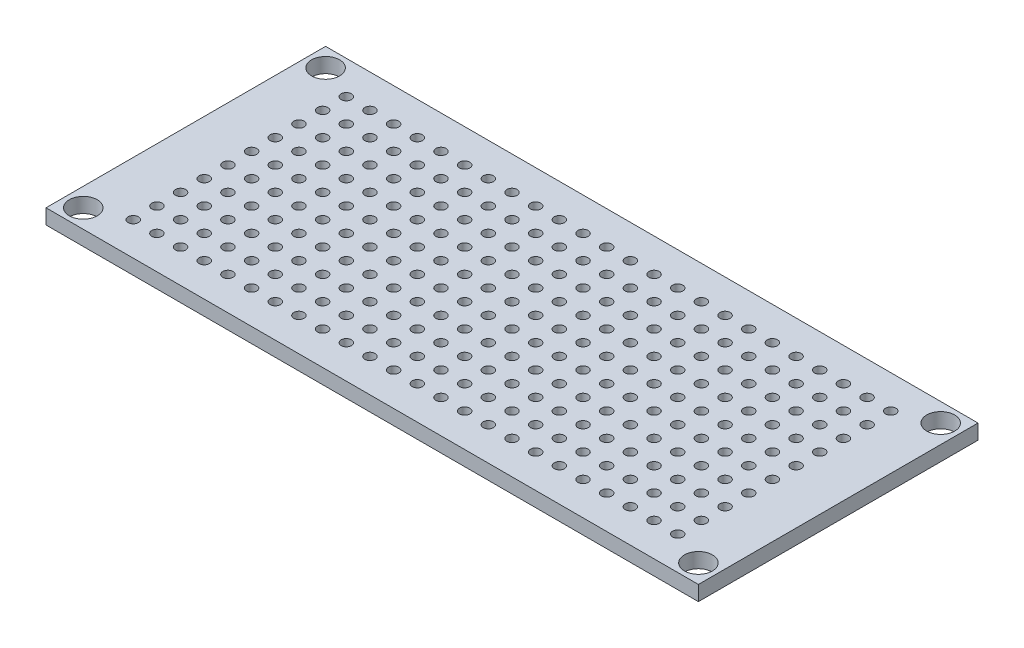
SolidWorks part; units mm, degrees
ref_plane "Front Plane" through (0, 0, 0) normal (0, 0, 1) x (1, 0, 0)
ref_plane "Top Plane" through (0, 0, 0) normal (0, 1, 0) x (1, 0, 0)
ref_plane "Right Plane" through (0, 0, 0) normal (1, 0, 0) x (0, 0, -1)
sketch "Sketch1" plane through (0, 0, 0) normal (0, 1, 0) x (1, 0, 0)
  line L0 (0, 15) -> (0, -15) construction
  line L1 (-35, 15) -> (35, 15)
  line L2 (-35, 15) -> (-35, -15)
  line L3 (-35, -15) -> (35, -15)
  line L4 (35, 15) -> (35, -15)
  line L5 (-35, 15) -> (35, -15) construction
  line L6 (-35, -15) -> (35, 15) construction
  line L7 (-35, 0) -> (35, 0) construction
  circle A0 centre (-33, 13) radius 1.5
  circle A1 centre (33, 13) radius 1.5
  circle A2 centre (33, -13) radius 1.5
  circle A3 centre (-33, -13) radius 1.5
  point P0 (0, 0)
  dimension "D5" = 3
  dimension "D1" = 70
  dimension "D2" = 30
  dimension "D3" = 66
  dimension "D4" = 26
extrude "Boss-Extrude1" add sketch "Sketch1" along normal blind 1.6
sketch "Sketch2" plane through (0, 1.6, 0) normal (0, 1, 0) x (1, 0, 0)
  line L0 (29.21, 11.43) -> (29.21, -11.43) construction
  line L1 (-35, 0) -> (35, 0) construction
  line L2 (-35, 15) -> (-35, -15) construction
  line L3 (35, -15) -> (35, 15) construction
  line L4 (-29.21, -11.43) -> (29.21, -11.43) construction
  line L5 (0, 15) -> (0, -15) construction
  line L6 (35, 15) -> (-35, 15) construction
  line L7 (-35, -15) -> (35, -15) construction
  line L8 (-29.21, 8.89) -> (-29.21, 11.43) construction
  line L9 (-29.21, 11.43) -> (-26.67, 11.43) construction
  circle A0 centre (-29.21, 11.43) radius 0.55
  circle A1 centre (-26.67, 11.43) radius 0.55
  circle A2 centre (-24.13, 11.43) radius 0.55
  circle A3 centre (-21.59, 11.43) radius 0.55
  circle A4 centre (-19.05, 11.43) radius 0.55
  circle A5 centre (-16.51, 11.43) radius 0.55
  circle A6 centre (-13.97, 11.43) radius 0.55
  circle A7 centre (-11.43, 11.43) radius 0.55
  circle A8 centre (-8.89, 11.43) radius 0.55
  circle A9 centre (-6.35, 11.43) radius 0.55
  circle A10 centre (-3.81, 11.43) radius 0.55
  circle A11 centre (-1.27, 11.43) radius 0.55
  circle A12 centre (1.27, 11.43) radius 0.55
  circle A13 centre (3.81, 11.43) radius 0.55
  circle A14 centre (6.35, 11.43) radius 0.55
  circle A15 centre (8.89, 11.43) radius 0.55
  circle A16 centre (11.43, 11.43) radius 0.55
  circle A17 centre (13.97, 11.43) radius 0.55
  circle A18 centre (16.51, 11.43) radius 0.55
  circle A19 centre (19.05, 11.43) radius 0.55
  circle A20 centre (21.59, 11.43) radius 0.55
  circle A21 centre (24.13, 11.43) radius 0.55
  circle A22 centre (26.67, 11.43) radius 0.55
  circle A23 centre (29.21, 11.43) radius 0.55
  circle A24 centre (-26.67, 8.89) radius 0.55
  circle A25 centre (-24.13, 8.89) radius 0.55
  circle A26 centre (-21.59, 8.89) radius 0.55
  circle A27 centre (-19.05, 8.89) radius 0.55
  circle A28 centre (-16.51, 8.89) radius 0.55
  circle A29 centre (-13.97, 8.89) radius 0.55
  circle A30 centre (-11.43, 8.89) radius 0.55
  circle A31 centre (-8.89, 8.89) radius 0.55
  circle A32 centre (-6.35, 8.89) radius 0.55
  circle A33 centre (-3.81, 8.89) radius 0.55
  circle A34 centre (-1.27, 8.89) radius 0.55
  circle A35 centre (1.27, 8.89) radius 0.55
  circle A36 centre (3.81, 8.89) radius 0.55
  circle A37 centre (6.35, 8.89) radius 0.55
  circle A38 centre (8.89, 8.89) radius 0.55
  circle A39 centre (11.43, 8.89) radius 0.55
  circle A40 centre (13.97, 8.89) radius 0.55
  circle A41 centre (16.51, 8.89) radius 0.55
  circle A42 centre (19.05, 8.89) radius 0.55
  circle A43 centre (21.59, 8.89) radius 0.55
  circle A44 centre (24.13, 8.89) radius 0.55
  circle A45 centre (26.67, 8.89) radius 0.55
  circle A46 centre (29.21, 8.89) radius 0.55
  circle A47 centre (-26.67, 6.35) radius 0.55
  circle A48 centre (-24.13, 6.35) radius 0.55
  circle A49 centre (-21.59, 6.35) radius 0.55
  circle A50 centre (-19.05, 6.35) radius 0.55
  circle A51 centre (-16.51, 6.35) radius 0.55
  circle A52 centre (-13.97, 6.35) radius 0.55
  circle A53 centre (-11.43, 6.35) radius 0.55
  circle A54 centre (-8.89, 6.35) radius 0.55
  circle A55 centre (-6.35, 6.35) radius 0.55
  circle A56 centre (-3.81, 6.35) radius 0.55
  circle A57 centre (-1.27, 6.35) radius 0.55
  circle A58 centre (1.27, 6.35) radius 0.55
  circle A59 centre (3.81, 6.35) radius 0.55
  circle A60 centre (6.35, 6.35) radius 0.55
  circle A61 centre (8.89, 6.35) radius 0.55
  circle A62 centre (11.43, 6.35) radius 0.55
  circle A63 centre (13.97, 6.35) radius 0.55
  circle A64 centre (16.51, 6.35) radius 0.55
  circle A65 centre (19.05, 6.35) radius 0.55
  circle A66 centre (21.59, 6.35) radius 0.55
  circle A67 centre (24.13, 6.35) radius 0.55
  circle A68 centre (26.67, 6.35) radius 0.55
  circle A69 centre (29.21, 6.35) radius 0.55
  circle A70 centre (-26.67, 3.81) radius 0.55
  circle A71 centre (-24.13, 3.81) radius 0.55
  circle A72 centre (-21.59, 3.81) radius 0.55
  circle A73 centre (-19.05, 3.81) radius 0.55
  circle A74 centre (-16.51, 3.81) radius 0.55
  circle A75 centre (-13.97, 3.81) radius 0.55
  circle A76 centre (-11.43, 3.81) radius 0.55
  circle A77 centre (-8.89, 3.81) radius 0.55
  circle A78 centre (-6.35, 3.81) radius 0.55
  circle A79 centre (-3.81, 3.81) radius 0.55
  circle A80 centre (-1.27, 3.81) radius 0.55
  circle A81 centre (1.27, 3.81) radius 0.55
  circle A82 centre (3.81, 3.81) radius 0.55
  circle A83 centre (6.35, 3.81) radius 0.55
  circle A84 centre (8.89, 3.81) radius 0.55
  circle A85 centre (11.43, 3.81) radius 0.55
  circle A86 centre (13.97, 3.81) radius 0.55
  circle A87 centre (16.51, 3.81) radius 0.55
  circle A88 centre (19.05, 3.81) radius 0.55
  circle A89 centre (21.59, 3.81) radius 0.55
  circle A90 centre (24.13, 3.81) radius 0.55
  circle A91 centre (26.67, 3.81) radius 0.55
  circle A92 centre (29.21, 3.81) radius 0.55
  circle A93 centre (-26.67, 1.27) radius 0.55
  circle A94 centre (-24.13, 1.27) radius 0.55
  circle A95 centre (-21.59, 1.27) radius 0.55
  circle A96 centre (-19.05, 1.27) radius 0.55
  circle A97 centre (-16.51, 1.27) radius 0.55
  circle A98 centre (-13.97, 1.27) radius 0.55
  circle A99 centre (-11.43, 1.27) radius 0.55
  circle A100 centre (-8.89, 1.27) radius 0.55
  circle A101 centre (-6.35, 1.27) radius 0.55
  circle A102 centre (-3.81, 1.27) radius 0.55
  circle A103 centre (-1.27, 1.27) radius 0.55
  circle A104 centre (1.27, 1.27) radius 0.55
  circle A105 centre (3.81, 1.27) radius 0.55
  circle A106 centre (6.35, 1.27) radius 0.55
  circle A107 centre (8.89, 1.27) radius 0.55
  circle A108 centre (11.43, 1.27) radius 0.55
  circle A109 centre (13.97, 1.27) radius 0.55
  circle A110 centre (16.51, 1.27) radius 0.55
  circle A111 centre (19.05, 1.27) radius 0.55
  circle A112 centre (21.59, 1.27) radius 0.55
  circle A113 centre (24.13, 1.27) radius 0.55
  circle A114 centre (26.67, 1.27) radius 0.55
  circle A115 centre (29.21, 1.27) radius 0.55
  circle A116 centre (-26.67, -1.27) radius 0.55
  circle A117 centre (-24.13, -1.27) radius 0.55
  circle A118 centre (-21.59, -1.27) radius 0.55
  circle A119 centre (-19.05, -1.27) radius 0.55
  circle A120 centre (-16.51, -1.27) radius 0.55
  circle A121 centre (-13.97, -1.27) radius 0.55
  circle A122 centre (-11.43, -1.27) radius 0.55
  circle A123 centre (-8.89, -1.27) radius 0.55
  circle A124 centre (-6.35, -1.27) radius 0.55
  circle A125 centre (-3.81, -1.27) radius 0.55
  circle A126 centre (-1.27, -1.27) radius 0.55
  circle A127 centre (1.27, -1.27) radius 0.55
  circle A128 centre (3.81, -1.27) radius 0.55
  circle A129 centre (6.35, -1.27) radius 0.55
  circle A130 centre (8.89, -1.27) radius 0.55
  circle A131 centre (11.43, -1.27) radius 0.55
  circle A132 centre (13.97, -1.27) radius 0.55
  circle A133 centre (16.51, -1.27) radius 0.55
  circle A134 centre (19.05, -1.27) radius 0.55
  circle A135 centre (21.59, -1.27) radius 0.55
  circle A136 centre (24.13, -1.27) radius 0.55
  circle A137 centre (26.67, -1.27) radius 0.55
  circle A138 centre (29.21, -1.27) radius 0.55
  circle A139 centre (-26.67, -3.81) radius 0.55
  circle A140 centre (-24.13, -3.81) radius 0.55
  circle A141 centre (-21.59, -3.81) radius 0.55
  circle A142 centre (-19.05, -3.81) radius 0.55
  circle A143 centre (-16.51, -3.81) radius 0.55
  circle A144 centre (-13.97, -3.81) radius 0.55
  circle A145 centre (-11.43, -3.81) radius 0.55
  circle A146 centre (-8.89, -3.81) radius 0.55
  circle A147 centre (-6.35, -3.81) radius 0.55
  circle A148 centre (-3.81, -3.81) radius 0.55
  circle A149 centre (-1.27, -3.81) radius 0.55
  circle A150 centre (1.27, -3.81) radius 0.55
  circle A151 centre (3.81, -3.81) radius 0.55
  circle A152 centre (6.35, -3.81) radius 0.55
  circle A153 centre (8.89, -3.81) radius 0.55
  circle A154 centre (11.43, -3.81) radius 0.55
  circle A155 centre (13.97, -3.81) radius 0.55
  circle A156 centre (16.51, -3.81) radius 0.55
  circle A157 centre (19.05, -3.81) radius 0.55
  circle A158 centre (21.59, -3.81) radius 0.55
  circle A159 centre (24.13, -3.81) radius 0.55
  circle A160 centre (26.67, -3.81) radius 0.55
  circle A161 centre (29.21, -3.81) radius 0.55
  circle A162 centre (-26.67, -6.35) radius 0.55
  circle A163 centre (-24.13, -6.35) radius 0.55
  circle A164 centre (-21.59, -6.35) radius 0.55
  circle A165 centre (-19.05, -6.35) radius 0.55
  circle A166 centre (-16.51, -6.35) radius 0.55
  circle A167 centre (-13.97, -6.35) radius 0.55
  circle A168 centre (-11.43, -6.35) radius 0.55
  circle A169 centre (-8.89, -6.35) radius 0.55
  circle A170 centre (-6.35, -6.35) radius 0.55
  circle A171 centre (-3.81, -6.35) radius 0.55
  circle A172 centre (-1.27, -6.35) radius 0.55
  circle A173 centre (1.27, -6.35) radius 0.55
  circle A174 centre (3.81, -6.35) radius 0.55
  circle A175 centre (6.35, -6.35) radius 0.55
  circle A176 centre (8.89, -6.35) radius 0.55
  circle A177 centre (11.43, -6.35) radius 0.55
  circle A178 centre (13.97, -6.35) radius 0.55
  circle A179 centre (16.51, -6.35) radius 0.55
  circle A180 centre (19.05, -6.35) radius 0.55
  circle A181 centre (21.59, -6.35) radius 0.55
  circle A182 centre (24.13, -6.35) radius 0.55
  circle A183 centre (26.67, -6.35) radius 0.55
  circle A184 centre (29.21, -6.35) radius 0.55
  circle A185 centre (-26.67, -8.89) radius 0.55
  circle A186 centre (-24.13, -8.89) radius 0.55
  circle A187 centre (-21.59, -8.89) radius 0.55
  circle A188 centre (-19.05, -8.89) radius 0.55
  circle A189 centre (-16.51, -8.89) radius 0.55
  circle A190 centre (-13.97, -8.89) radius 0.55
  circle A191 centre (-11.43, -8.89) radius 0.55
  circle A192 centre (-8.89, -8.89) radius 0.55
  circle A193 centre (-6.35, -8.89) radius 0.55
  circle A194 centre (-3.81, -8.89) radius 0.55
  circle A195 centre (-1.27, -8.89) radius 0.55
  circle A196 centre (1.27, -8.89) radius 0.55
  circle A197 centre (3.81, -8.89) radius 0.55
  circle A198 centre (6.35, -8.89) radius 0.55
  circle A199 centre (8.89, -8.89) radius 0.55
  circle A200 centre (11.43, -8.89) radius 0.55
  circle A201 centre (13.97, -8.89) radius 0.55
  circle A202 centre (16.51, -8.89) radius 0.55
  circle A203 centre (19.05, -8.89) radius 0.55
  circle A204 centre (21.59, -8.89) radius 0.55
  circle A205 centre (24.13, -8.89) radius 0.55
  circle A206 centre (26.67, -8.89) radius 0.55
  circle A207 centre (29.21, -8.89) radius 0.55
  circle A208 centre (-26.67, -11.43) radius 0.55
  circle A209 centre (-24.13, -11.43) radius 0.55
  circle A210 centre (-21.59, -11.43) radius 0.55
  circle A211 centre (-19.05, -11.43) radius 0.55
  circle A212 centre (-16.51, -11.43) radius 0.55
  circle A213 centre (-13.97, -11.43) radius 0.55
  circle A214 centre (-11.43, -11.43) radius 0.55
  circle A215 centre (-8.89, -11.43) radius 0.55
  circle A216 centre (-6.35, -11.43) radius 0.55
  circle A217 centre (-3.81, -11.43) radius 0.55
  circle A218 centre (-1.27, -11.43) radius 0.55
  circle A219 centre (1.27, -11.43) radius 0.55
  circle A220 centre (3.81, -11.43) radius 0.55
  circle A221 centre (6.35, -11.43) radius 0.55
  circle A222 centre (8.89, -11.43) radius 0.55
  circle A223 centre (11.43, -11.43) radius 0.55
  circle A224 centre (13.97, -11.43) radius 0.55
  circle A225 centre (16.51, -11.43) radius 0.55
  circle A226 centre (19.05, -11.43) radius 0.55
  circle A227 centre (21.59, -11.43) radius 0.55
  circle A228 centre (24.13, -11.43) radius 0.55
  circle A229 centre (26.67, -11.43) radius 0.55
  circle A230 centre (29.21, -11.43) radius 0.55
  circle A231 centre (-29.21, 8.89) radius 0.55
  circle A232 centre (-29.21, 6.35) radius 0.55
  circle A233 centre (-29.21, 3.81) radius 0.55
  circle A234 centre (-29.21, 1.27) radius 0.55
  circle A235 centre (-29.21, -1.27) radius 0.55
  circle A236 centre (-29.21, -3.81) radius 0.55
  circle A237 centre (-29.21, -6.35) radius 0.55
  circle A238 centre (-29.21, -8.89) radius 0.55
  circle A239 centre (-29.21, -11.43) radius 0.55
  point P486 (29.21, 0)
  point P487 (0, -11.43)
  dimension "D1" = 1.1
  dimension "D4" = 2.54
  dimension "D2" = 24
  dimension "D3" = 10
extrude "Cut-Extrude1" cut sketch "Sketch2" against normal up to next (1.6 mm away)
